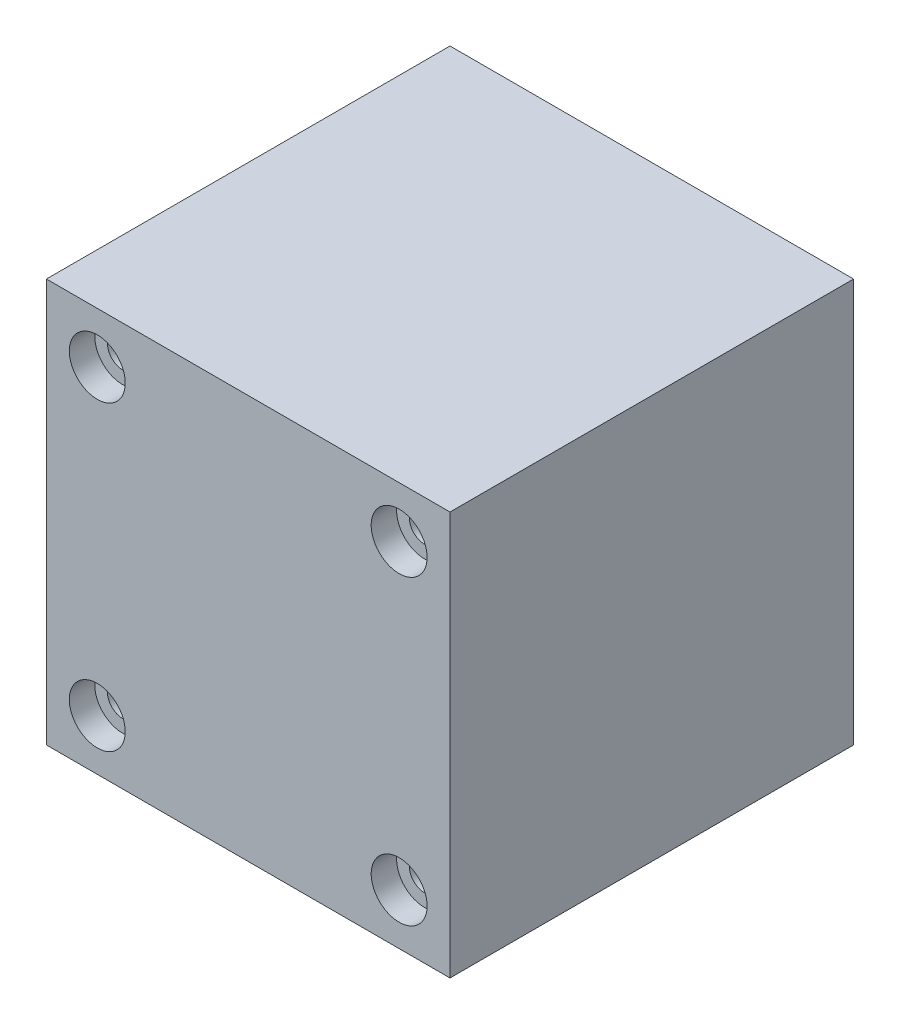
SolidWorks part; units mm, degrees
material "1060 Alloy"
ref_plane "Front Plane" through (0, 0, 0) normal (0, 0, 1) x (1, 0, 0)
ref_plane "Top Plane" through (0, 0, 0) normal (0, 1, 0) x (1, 0, 0)
ref_plane "Right Plane" through (0, 0, 0) normal (1, 0, 0) x (0, 0, -1)
sketch "Sketch1" plane through (0, 0, 0) normal (0, 0, 1) x (1, 0, 0)
  line L1 (-15.875, -15.875) -> (15.875, -15.875)
  line L2 (-15.875, -15.875) -> (-15.875, 15.875)
  line L3 (-15.875, 15.875) -> (15.875, 15.875)
  line L4 (15.875, -15.875) -> (15.875, 15.875)
  line L5 (-15.875, -15.875) -> (15.875, 15.875) construction
  line L6 (-15.875, 15.875) -> (15.875, -15.875) construction
  point P0 (0, 0)
  dimension "D1" = 31.75
  dimension "D2" = 31.75
extrude "Boss-Extrude1" add sketch "Sketch1" along normal blind 31.75
hole_wizard "CBORE for M2 SHCS1" positions "Sketch3" profile "Sketch4" counterbore size "M2" standard "ANSI Metric" end condition through all
sketch "Sketch3" plane through (0, 0, 31.75) normal (0, 0, 1) x (1, 0, 0)
  line L0 (-11.875, 11.875) -> (-11.875, -11.875) construction
  line L1 (-11.875, -11.875) -> (11.875, -11.875) construction
  line L2 (11.875, -11.875) -> (11.875, 11.875) construction
  line L3 (11.875, 11.875) -> (-11.875, 11.875) construction
  line L5 (15.875, 15.875) -> (-15.875, 15.875) construction
  line L6 (-15.875, -15.875) -> (15.875, -15.875) construction
  line L7 (-15.875, 15.875) -> (-15.875, -15.875) construction
  line L8 (15.875, -15.875) -> (15.875, 15.875) construction
  point P0 (-11.875, 11.875)
  point P2 (11.875, 11.875)
  point P4 (11.875, -11.875)
  point P6 (-11.875, -11.875)
  dimension "D1" = 4
  dimension "D2" = 4
  dimension "D3" = 4
  dimension "D4" = 4
sketch "Sketch4" plane through (-11.875, 11.875, 31.75) normal (1, 0, 0) x (0, -1, 0)
  line L0 (0, 0) -> (0, 31.75)
  line L1 (0, 31.75) -> (1.2, 31.75)
  line L3 (1.2, 31.75) -> (1.2, 2)
  line L4 (1.2, 2) -> (2.2, 2)
  line L5 (2.2, 2) -> (2.2, 0)
  line L7 (2.2, 0) -> (0, 0)
  line L11 (0, -6.35) -> (0, 107.95) construction
  dimension "Thru Hole Dia." = 2.4
  dimension "Thru Hole Depth" = 31.75
  dimension "C'Bore Dia." = 4.4
  dimension "C'Bore Depth" = 2
